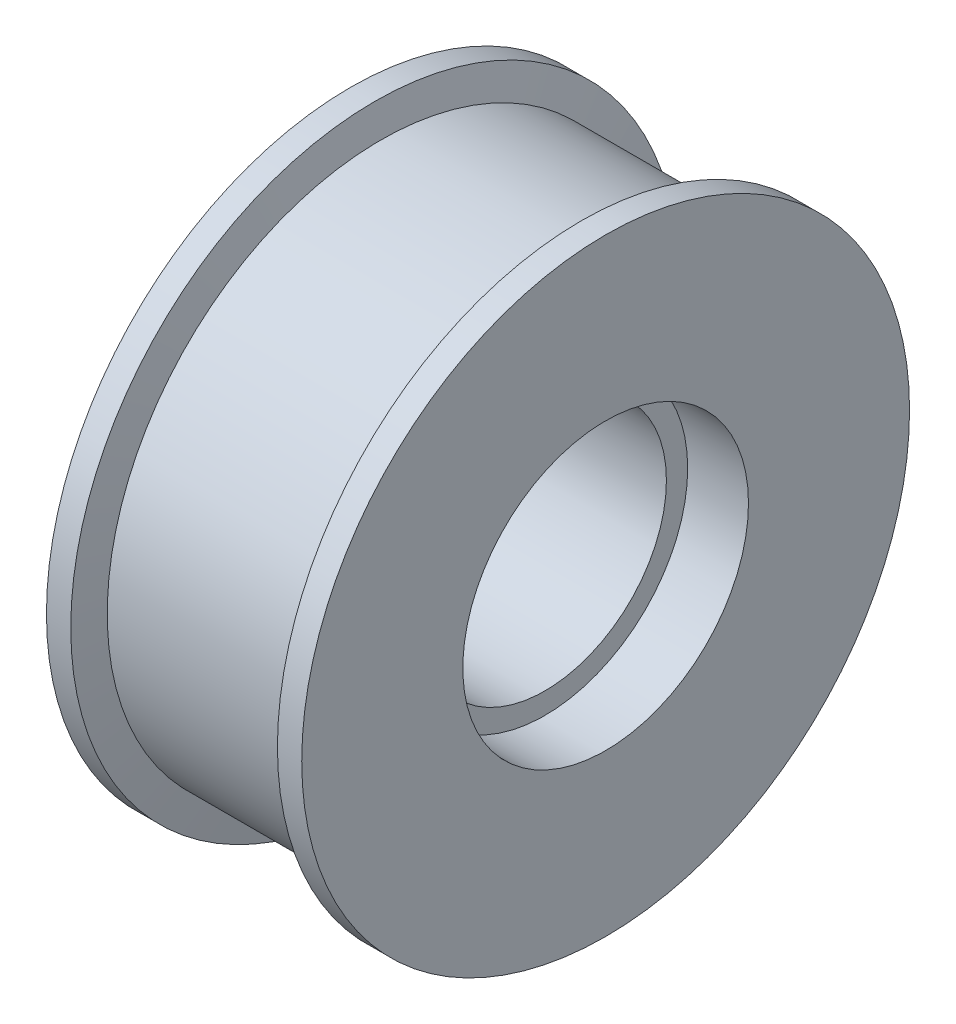
SolidWorks part; units mm, degrees
material "AISI 1045 钢，冷拔"
ref_plane "前视基准面" through (0, 0, 0) normal (0, 0, 1) x (1, 0, 0)
ref_plane "上视基准面" through (0, 0, 0) normal (0, 1, 0) x (1, 0, 0)
ref_plane "右视基准面" through (0, 0, 0) normal (1, 0, 0) x (0, 0, -1)
sketch "草图1" plane through (0, -730.3692, 693.6022) normal (0, -0.7251, 0.6886) x (-1, 0, 0)
  line L0 (-32.8924, 64.4673) -> (-32.8924, 90.9673)
  line L1 (9.1076, 90.9673) -> (9.1076, 64.4673)
  line L2 (-32.8924, 90.9673) -> (-28.8924, 90.9673)
  line L3 (-28.8924, 90.9673) -> (-27.8924, 85.9673)
  line L4 (-27.8924, 85.9673) -> (4.1076, 85.9673)
  line L5 (4.1076, 85.9673) -> (5.1076, 90.9673)
  line L6 (5.1076, 90.9673) -> (9.1076, 90.9673)
  line L7 (-43.9031, 40.9673) -> (29.7325, 40.9673) construction
  line L8 (-32.8924, 64.4673) -> (-22.8924, 64.4673)
  line L9 (-22.8924, 64.4673) -> (-22.8924, 60.9673)
  line L10 (-22.8924, 60.9673) -> (-0.8924, 60.9673)
  line L11 (-0.8924, 60.9673) -> (-0.8924, 64.4673)
  line L12 (-0.8924, 64.4673) -> (9.1076, 64.4673)
  dimension "D1" = 4
  dimension "D2" = 5
  dimension "D3" = 4
  dimension "D4" = 5
  dimension "D5" = 32
  dimension "D6" = 45
  dimension "D7" = 5
  dimension "D8" = 5
  dimension "D9" = 10
  dimension "D10" = 10
  dimension "D11" = 23.5
  dimension "D12" = 23.5
  dimension "D13" = 20
revolve "旋转1" add sketch "草图1" angle 360 about L7
